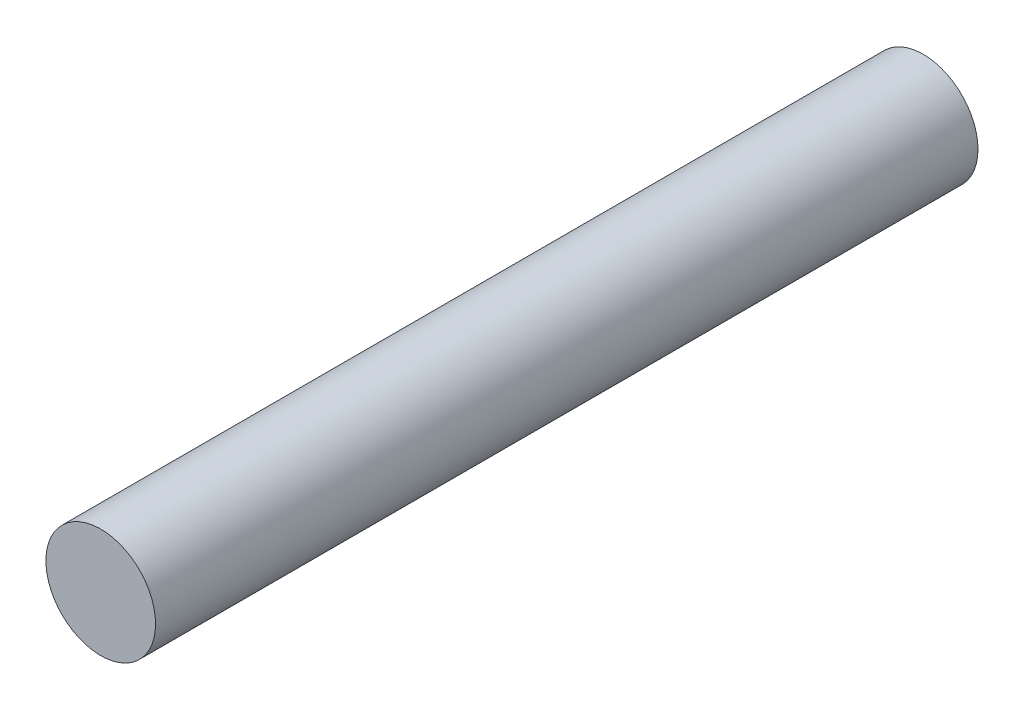
SolidWorks part; units mm, degrees
ref_plane "Front Plane" through (0, 0, 0) normal (0, 0, 1) x (1, 0, 0)
ref_plane "Top Plane" through (0, 0, 0) normal (0, 1, 0) x (1, 0, 0)
ref_plane "Right Plane" through (0, 0, 0) normal (1, 0, 0) x (0, 0, -1)
sketch "Sketch1" plane through (0, 0, 0) normal (0, 0, 1) x (1, 0, 0)
  circle A0 centre (0, 0) radius 4
  dimension "D1" = 8
extrude "Boss-Extrude1" add sketch "Sketch1" along normal blind 60
